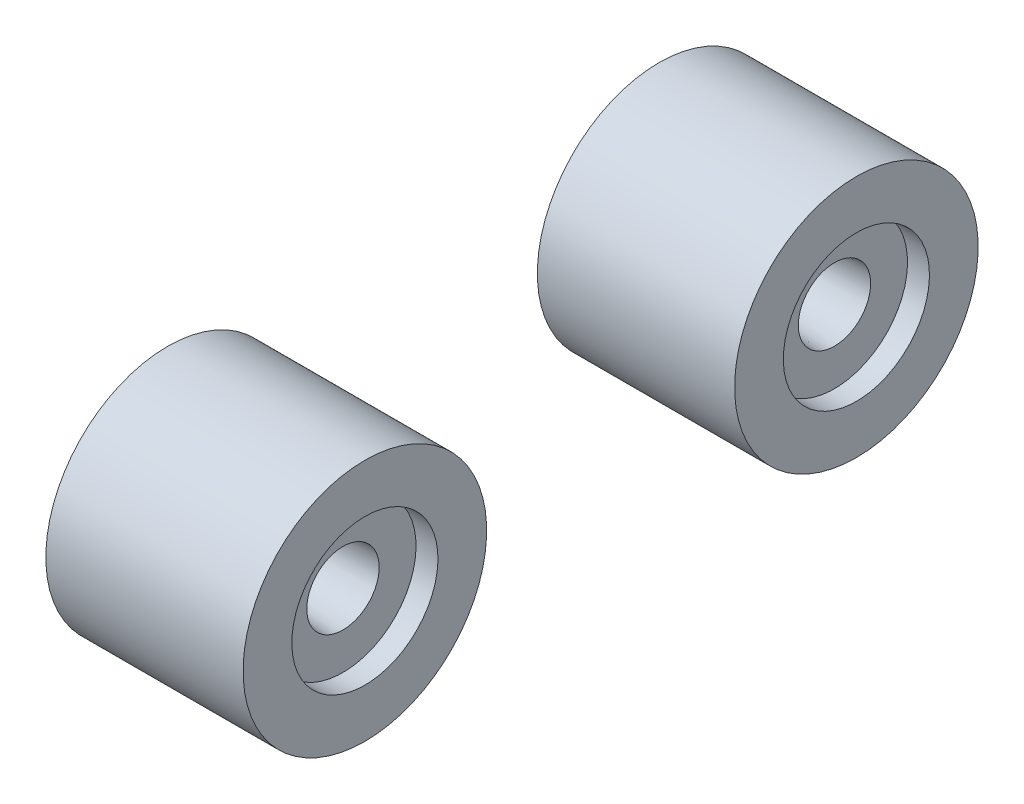
SolidWorks part; units mm, degrees
ref_plane "Front Plane" through (0, 0, 0) normal (0, 0, 1) x (1, 0, 0)
ref_plane "Top Plane" through (0, 0, 0) normal (0, 1, 0) x (1, 0, 0)
ref_plane "Right Plane" through (0, 0, 0) normal (1, 0, 0) x (0, 0, -1)
sketch "Sketch1" plane through (0, 0, 0) normal (0, 0, 1) x (1, 0, 0)
  line L0 (8.255, 0) -> (-8.255, 0) construction
  line L1 (26.255, 0) -> (-26.255, 0) construction
  line L2 (8.255, 0) -> (8.255, 12.5)
  line L3 (8.255, 12.5) -> (26.255, 12.5)
  line L4 (26.255, 12.5) -> (26.255, 0)
  line L5 (8.255, 0) -> (26.255, 0)
  point P4 (0, 0)
  point P8 (0, 0)
  dimension "D1" = 18
  dimension "D2" = 16.51
  dimension "D3" = 12.5
revolve "Revolve1" add sketch "Sketch1" angle 360 about L5
sketch "Sketch2" plane through (8.255, 0, 0) normal (-1, 0, 0) x (0, 0, 1)
  circle A0 centre (0, 0) radius 3.7138
  dimension "D1" = 7.4275
extrude "Cut-Extrude1" cut sketch "Sketch2" against normal blind 7.5725 draft 3
sketch "Sketch3" plane through (26.255, 0, 0) normal (1, 0, 0) x (0, 0, -1)
  line L0 (-20.8953, -55) -> (-20.8953, -46.1532)
  line L1 (13.175, -55) -> (-13.175, -55) construction
  line L2 (13.175, -55) -> (13.175, 55) construction
  line L3 (13.175, 55) -> (-13.175, 55) construction
  line L4 (-13.175, -55) -> (-13.175, 55) construction
  line L5 (13.175, -55) -> (-13.175, 55) construction
  line L6 (13.175, 55) -> (-13.175, -55) construction
  line L7 (-24.3823, -32.1152) -> (-32.3245, -17.1152)
  line L9 (-5.4548, -55) -> (-5.4548, -44)
  line L11 (5.4547, -44) -> (5.4547, -55)
  line L12 (20.8953, -55) -> (20.8953, -46.1532)
  line L13 (24.3823, -32.1152) -> (32.3245, -17.1152)
  line L14 (9.9, 0) -> (-9.9, 0) construction
  line L15 (13.175, -55) -> (-13.175, 55) construction
  line L16 (13.175, 55) -> (-13.175, -55) construction
  line L17 (13.175, 55) -> (-13.175, 55) construction
  line L18 (24.3823, 32.1152) -> (32.3245, 17.1152)
  line L19 (20.8953, 55) -> (20.8953, 46.1532)
  line L20 (5.4547, 44) -> (5.4547, 55)
  line L21 (-5.4548, 55) -> (-5.4548, 44)
  line L22 (-24.3823, 32.1152) -> (-32.3245, 17.1152)
  line L23 (-20.8953, 55) -> (-20.8953, 46.1532)
  arc A15 (32.3245, -17.1152) -> (32.3245, 17.1152) centre (0, 0) ccw
  arc A16 (-5.4548, 55) -> (-20.8953, 55) centre (-13.175, 55) ccw
  arc A17 (-20.8953, -55) -> (-5.4548, -55) centre (-13.175, -55) ccw
  arc A18 (5.4547, -55) -> (20.8953, -55) centre (13.175, -55) ccw
  arc A19 (20.8953, 55) -> (5.4547, 55) centre (13.175, 55) ccw
  arc A20 (-5.4548, -44) -> (5.4547, -44) centre (0, -44) cw
  arc A21 (20.8953, -46.1532) -> (24.3823, -32.1152) centre (50.8953, -46.1532) cw
  arc A22 (-20.8953, -46.1532) -> (-24.3823, -32.1152) centre (-50.8953, -46.1532) ccw
  arc A23 (-20.8953, 46.1532) -> (-24.3823, 32.1152) centre (-50.8953, 46.1532) cw
  arc A24 (20.8953, 46.1532) -> (24.3823, 32.1152) centre (50.8953, 46.1532) ccw
  arc A25 (-5.4548, 44) -> (5.4547, 44) centre (0, 44) ccw
  arc A26 (5.4547, 55) -> (20.8953, 55) centre (13.175, 55) cw
  arc A27 (-20.8953, 55) -> (-5.4548, 55) centre (-13.175, 55) cw
  arc A29 (-32.3245, 17.1152) -> (-32.3245, -17.1152) centre (0, 0) ccw
  dimension "D3" = 15.4405
  dimension "D5" = 7.7203
  dimension "D4" = 30
  dimension "D7" = 15
  dimension "D9" = 110
  dimension "D1" = 73.152
  dimension "D6" = 15
  dimension "D2" = 26.35
  dimension "D8" = 11
sketch "Sketch4" plane through (26.255, 0, 0) normal (1, 0, 0) x (0, 0, -1)
  circle A0 centre (0, 0) radius 3.7138
  dimension "D1" = 7.4275
extrude "Cut-Extrude2" cut sketch "Sketch4" against normal blind 7.0725 draft 3
move or copy body "Body-Move/Copy1" bodies to move or copy 114 copy yes number of copies 1 translate (0, 0, 50.4528)
sketch "Sketch5" plane through (26.255, 0, 0) normal (1, 0, 0) x (0, 0, -1)
  circle A0 centre (0, 0) radius 12.5 construction
  circle A1 centre (0, 0) radius 12.5
  circle A2 centre (0, 0) radius 7.5
  circle A3 centre (-50.4528, 0) radius 12.5
  circle A4 centre (-50.4528, 0) radius 7.5
  circle A5 centre (-50.4528, 0) radius 12.5 construction
  dimension "D1" = 15
extrude "Boss-Extrude1" add sketch "Sketch5" along normal blind 2.25
combine bodies "Combine1" operation type add bodies to combine 115 117
